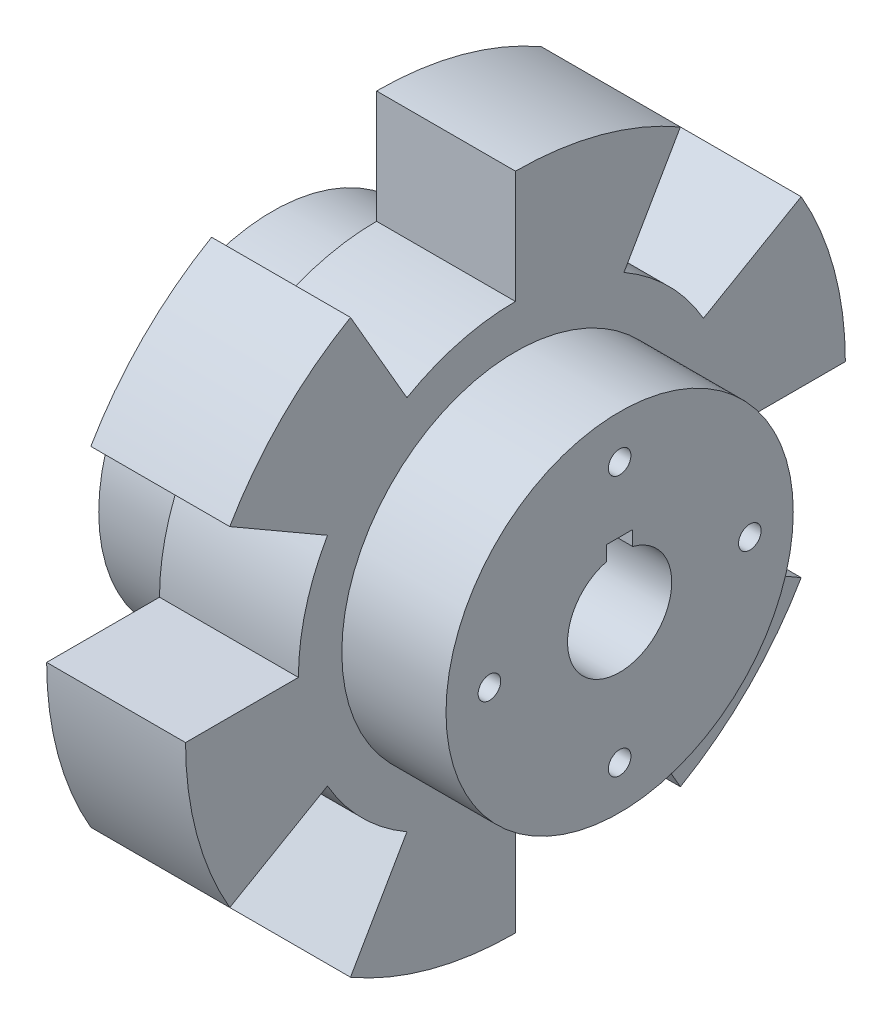
SolidWorks part; units mm, degrees
material "6063-T6"
ref_plane "Plano frontal" through (0, 0, 0) normal (0, 0, 1) x (1, 0, 0)
ref_plane "Plano superior" through (0, 0, 0) normal (0, 1, 0) x (1, 0, 0)
ref_plane "Plano direito" through (0, 0, 0) normal (1, 0, 0) x (0, 0, -1)
sketch "Esboço1" plane through (0, 0, 0) normal (0, 0, 1) x (1, 0, 0)
  line L0 (0, 0) -> (12, 0)
  line L1 (12, 0) -> (12, 18)
  line L2 (12, 18) -> (28, 18)
  line L3 (28, 18) -> (28, 0)
  line L4 (28, 0) -> (40, 0)
  line L5 (0, 0) -> (0, -20)
  line L6 (40, 0) -> (40, -20)
  line L7 (0, -20) -> (40, -20)
  dimension "D1" = 40
revolve "Revolução1" add sketch "Esboço1" angle 360 about L7
sketch "Esboço2" plane through (0, 0, 0) normal (-1, 0, 0) x (0, 0, 1)
  circle A0 centre (0, -20) radius 6
extrude "Corte-extrusão1" cut sketch "Esboço2" against normal through all
sketch "Esboço4" plane through (12, 0, 0) normal (-1, 0, 0) x (0, 0, 1)
sketch "Esboço8" plane through (0, 0, 0) normal (-1, 0, 0) x (0, 0, 1)
  line L1 (0, -12.5) -> (1.5, -12.5)
  line L2 (1.5, -12.5) -> (1.5, -14.6535)
  line L3 (1.5, -14.6535) -> (-1.5, -14.6535)
  line L4 (-1.5, -14.6535) -> (-1.5, -12.5)
  line L5 (-1.5, -12.5) -> (0, -12.5)
extrude "Corte-extrusão7" cut sketch "Esboço8" against normal through all
sketch "Esboço9" plane through (12, 0, 0) normal (-1, 0, 0) x (0, 0, 1)
  line L0 (0, -58) -> (0, -45)
  line L13 (-19, -52.909) -> (-12.5, -41.6506)
  line L14 (19, 12.909) -> (12.5, 1.6506)
  line L15 (0, 18) -> (0, 5)
  line L16 (-19, 12.909) -> (-12.5, 1.6506)
  line L17 (-32.909, -1) -> (-21.6506, -7.5)
  line L18 (32.909, -1) -> (21.6506, -7.5)
  line L19 (19, -52.909) -> (12.5, -41.6506)
  line L20 (32.909, -39) -> (21.6506, -32.5)
  line L21 (38, -20) -> (25, -20)
  line L22 (-38, -20) -> (-25, -20)
  line L23 (-32.909, -39) -> (-21.6506, -32.5)
  arc A0 (-21.6506, -7.5) -> (-12.5, 1.6506) centre (0, -20) cw
  arc A2 (0, 5) -> (12.5, 1.6506) centre (0, -20) cw
  arc A3 (21.6506, -7.5) -> (25, -20) centre (0, -20) cw
  arc A4 (21.6506, -32.5) -> (12.5, -41.6506) centre (0, -20) cw
  arc A5 (0, -45) -> (-12.5, -41.6506) centre (0, -20) cw
  arc A6 (-25, -20) -> (-21.6506, -32.5) centre (0, -20) ccw
  arc A7 (-32.909, -39) -> (-38, -20) centre (0, -20) cw
  arc A8 (-32.909, -1) -> (-19, 12.909) centre (0, -20) cw
  arc A9 (32.909, -1) -> (38, -20) centre (0, -20) cw
  arc A10 (-19, -52.909) -> (0, -58) centre (0, -20) ccw
  arc A11 (0, 18) -> (19, 12.909) centre (0, -20) cw
  arc A12 (19, -52.909) -> (32.909, -39) centre (0, -20) ccw
extrude "Corte-extrusão8" cut sketch "Esboço9" against normal through all
sketch "Esboço10" plane through (0, 0, 0) normal (-1, 0, 0) x (0, 0, 1)
  circle A1 centre (0, -5.004) radius 1.3
  circle A2 centre (14.996, -20) radius 1.3
  circle A3 centre (0, -34.996) radius 1.3
  circle A4 centre (-14.996, -20) radius 1.3
extrude "Corte-extrusão9" cut sketch "Esboço10" against normal through all
